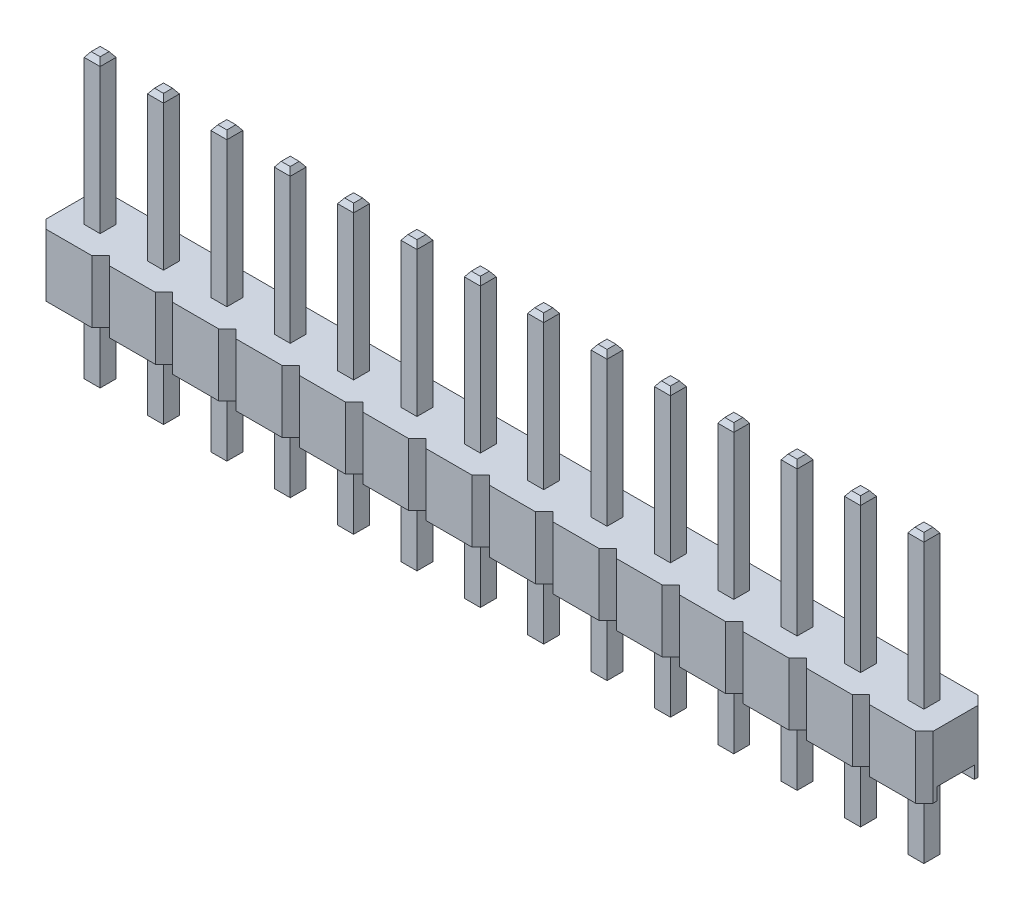
SolidWorks part; units mm, degrees
ref_plane "Front Plane" through (0, 0, 0) normal (0, 0, 1) x (1, 0, 0)
ref_plane "Top Plane" through (0, 0, 0) normal (0, 1, 0) x (1, 0, 0)
ref_plane "Right Plane" through (0, 0, 0) normal (1, 0, 0) x (0, 0, -1)
sketch "Sketch1" plane through (0, 0, 0) normal (0, 1, 0) x (1, 0, 0)
  line L0 (0, 2.15) -> (0.35, 2.5)
  line L1 (0.35, 0) -> (2.19, 0)
  line L2 (0, 0.35) -> (0, 2.15)
  line L3 (0.35, 2.5) -> (2.19, 2.5)
  line L4 (2.54, 0.35) -> (2.54, 2.15)
  line L5 (2.19, 2.5) -> (2.54, 2.15)
  line L6 (2.19, 0) -> (2.54, 0.35)
  line L7 (0, 0.35) -> (0.35, 0)
  point P0 (0, 0)
  point P1 (2.54, 2.5)
  point P2 (0, 2.5)
  point P3 (2.54, 0)
  dimension "D1" = 2.5
  dimension "D2" = 2.54
extrude "Boss-Extrude1" add sketch "Sketch1" along normal blind 2.5
sketch "Sketch3" plane through (0, 0, 0) normal (0, -1, 0) x (1, 0, 0)
  line L0 (0, -1.25) -> (2.54, -1.25) construction
  line L1 (0, -2.15) -> (0, -0.35) construction
  line L2 (2.54, -0.35) -> (2.54, -2.15) construction
  line L4 (0, -2) -> (2.54, -2)
  line L5 (0, -2) -> (0, -0.5)
  line L6 (0, -0.5) -> (2.54, -0.5)
  line L7 (2.54, -2) -> (2.54, -0.5)
  line L8 (0, -2) -> (2.54, -0.5) construction
  line L9 (0, -0.5) -> (2.54, -2) construction
  point P6 (1.27, -1.25)
  dimension "D1" = 1.5
extrude "Cut-Extrude1" cut sketch "Sketch3" against normal blind 0.5
sketch "Sketch4" plane through (0, 2.5, 0) normal (0, 1, 0) x (1, 0, 0)
  line L0 (0, 1.25) -> (2.54, 1.25) construction
  line L1 (0, 2.15) -> (0, 0.35) construction
  line L2 (2.54, 0.35) -> (2.54, 2.15) construction
  line L4 (0.95, 0.93) -> (1.59, 0.93)
  line L5 (0.95, 0.93) -> (0.95, 1.57)
  line L6 (0.95, 1.57) -> (1.59, 1.57)
  line L7 (1.59, 0.93) -> (1.59, 1.57)
  line L8 (0.95, 0.93) -> (1.59, 1.57) construction
  line L9 (0.95, 1.57) -> (1.59, 0.93) construction
  point P6 (1.27, 1.25)
  dimension "D1" = 0.64
extrude "Boss-Extrude2" add sketch "Sketch4" along normal blind 6 and the other way blind 5.5
chamfer "Chamfer1" distance 0.2 angle 35 8 edges at (1.27, -3, -1.57) (0.95, -3, -1.25) (1.27, -3, -0.93) (1.59, -3, -1.25) (1.27, 8.5, -0.93) (0.95, 8.5, -1.25) (1.27, 8.5, -1.57) (1.59, 8.5, -1.25)
pattern_linear "LPattern3" count 14 spacing 2.54 along (-1, 0, 0) of "Boss-Extrude1", "Cut-Extrude1", "Boss-Extrude2", "Chamfer1"
